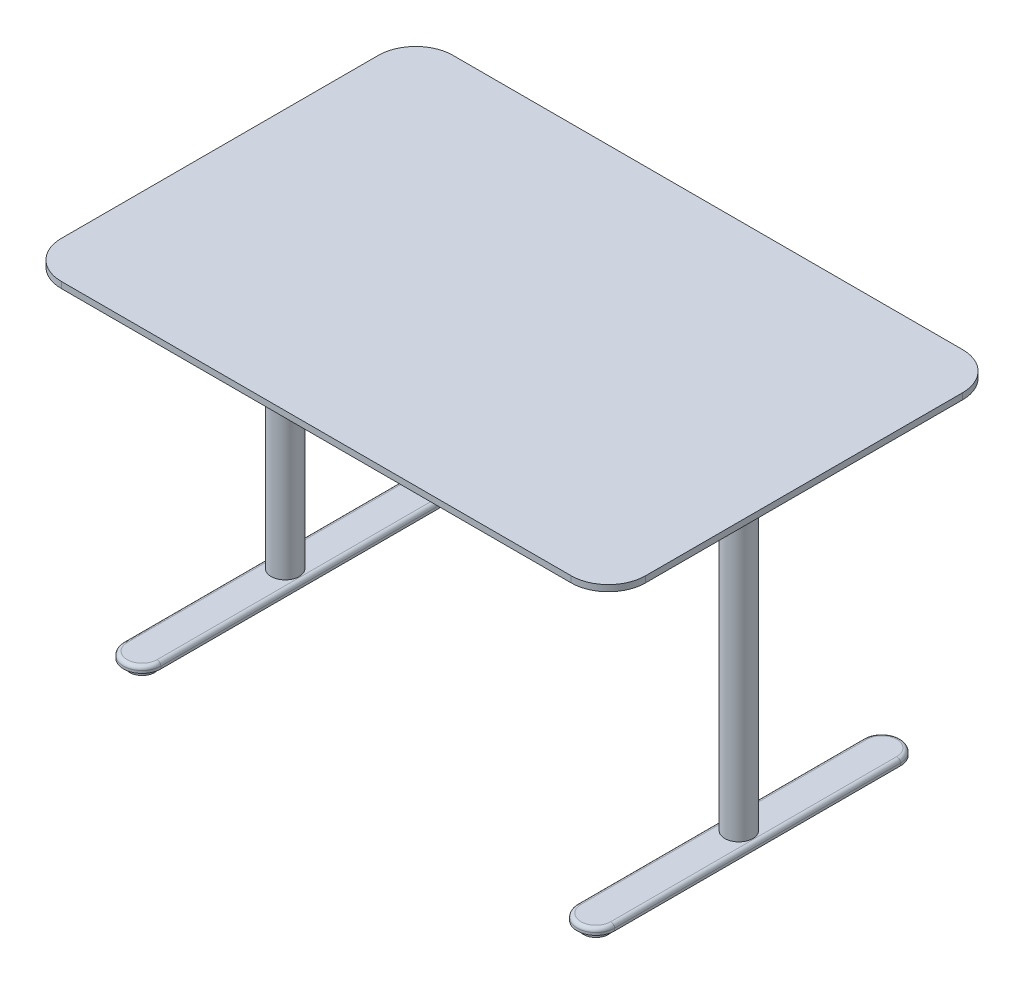
SolidWorks part; units mm, degrees
ref_plane "Front Plane" through (0, 0, 0) normal (0, 0, 1) x (1, 0, 0)
ref_plane "Top Plane" through (0, 0, 0) normal (0, 1, 0) x (1, 0, 0)
ref_plane "Right Plane" through (0, 0, 0) normal (1, 0, 0) x (0, 0, -1)
sketch "Sketch1" plane through (0, 0, 0) normal (0, 1, 0) x (1, 0, 0)
  line L1 (-520.7, 400.05) -> (520.7, 400.05)
  line L2 (-596.9, 323.85) -> (-596.9, -323.85)
  line L3 (-520.7, -400.05) -> (520.7, -400.05)
  line L4 (596.9, 323.85) -> (596.9, -323.85)
  line L5 (-596.9, 400.05) -> (596.9, -400.05) construction
  line L6 (-596.9, -400.05) -> (596.9, 400.05) construction
  arc A0 (-596.9, -323.85) -> (-520.7, -400.05) centre (-520.7, -323.85) ccw
  arc A1 (520.7, -400.05) -> (596.9, -323.85) centre (520.7, -323.85) ccw
  arc A2 (520.7, 400.05) -> (596.9, 323.85) centre (520.7, 323.85) cw
  arc A3 (-520.7, 400.05) -> (-596.9, 323.85) centre (-520.7, 323.85) ccw
  point P0 (0, 0)
  dimension "D3" = 76.2
  dimension "D1" = 1193.8
  dimension "D2" = 800.1
extrude "Boss-Extrude1" add sketch "Sketch1" against normal blind 12.7
sketch "Sketch2" plane through (0, -12.7, 0) normal (0, -1, 0) x (1, 0, 0)
  line L1 (-527.05, 228.6) -> (527.05, 228.6)
  line L2 (-527.05, 228.6) -> (-527.05, -228.6)
  line L3 (-527.05, -228.6) -> (527.05, -228.6)
  line L4 (527.05, 228.6) -> (527.05, -228.6)
  line L5 (-527.05, 228.6) -> (527.05, -228.6) construction
  line L6 (-527.05, -228.6) -> (527.05, 228.6) construction
  point P0 (0, 0)
  dimension "D1" = 1054.1
  dimension "D2" = 457.2
extrude "Extrude-Thin1" add sketch "Sketch2" along normal blind 31.75 separate body thin
sketch "Sketch3" plane through (0, -44.45, 0) normal (0, -1, 0) x (1, 0, 0)
  line L0 (-495.3, -196.85) -> (495.3, -196.85) construction
  line L1 (-431.8, 196.85) -> (-400.05, 196.85)
  line L2 (-431.8, 196.85) -> (-431.8, -196.85)
  line L3 (-431.8, -196.85) -> (-400.05, -196.85)
  line L4 (-400.05, 196.85) -> (-400.05, -196.85)
  line L5 (0, 0) -> (0, 443.3) construction
  line L6 (-495.3, 196.85) -> (-495.3, -196.85) construction
  line L7 (495.3, 196.85) -> (-495.3, 196.85) construction
  line L8 (400.05, 196.85) -> (400.05, -196.85)
  line L9 (431.8, -196.85) -> (400.05, -196.85)
  line L10 (431.8, 196.85) -> (431.8, -196.85)
  line L11 (431.8, 196.85) -> (400.05, 196.85)
  point P11 (-400.05, 196.85)
  dimension "D1" = 31.75
  dimension "D2" = 63.5
extrude "Boss-Extrude3" add sketch "Sketch3" against normal up to surface (31.75 mm away) separate body up to face at (0, -12.7, 0)
sketch "Sketch4" plane through (0, -44.45, 0) normal (0, -1, 0) x (1, 0, 0)
  line L0 (-495.3, 196.85) -> (-495.3, -196.85) construction
  line L1 (-495.3, 44.45) -> (-431.8, 44.45)
  line L2 (-495.3, 44.45) -> (-495.3, -44.45)
  line L3 (-495.3, -44.45) -> (-431.8, -44.45)
  line L4 (-431.8, 44.45) -> (-431.8, -44.45)
  line L5 (-431.8, 196.85) -> (-431.8, -196.85) construction
  line L6 (-431.8, 0) -> (0, 0) construction
  line L7 (0, 0) -> (0, 156.5821) construction
  line L8 (431.8, 44.45) -> (431.8, -44.45)
  line L9 (495.3, -44.45) -> (431.8, -44.45)
  line L10 (495.3, 44.45) -> (495.3, -44.45)
  line L11 (495.3, 44.45) -> (431.8, 44.45)
  dimension "D1" = 88.9
extrude "Boss-Extrude4" add sketch "Sketch4" against normal blind 12.7 separate body
sketch "Sketch5" plane through (0, -44.45, 0) normal (0, -1, 0) x (1, 0, 0)
  line L0 (-463.55, 44.45) -> (-463.55, -44.45) construction
  line L1 (-431.8, 44.45) -> (-495.3, 44.45) construction
  line L2 (-495.3, -44.45) -> (-431.8, -44.45) construction
  line L3 (-463.55, 0) -> (0, 0) construction
  line L4 (0, 0) -> (0, 436.3226) construction
  circle A0 centre (-463.55, 0) radius 28.575
  circle A1 centre (463.55, 0) radius 28.575
  dimension "D1" = 57.15
extrude "Boss-Extrude5" add sketch "Sketch5" along normal blind 635 separate body
sketch "Sketch6" plane through (0, -679.45, 0) normal (0, -1, 0) x (1, 0, 0)
  line L0 (-463.55, -292.1) -> (-463.55, 292.1) construction
  line L1 (-501.65, -292.1) -> (-501.65, 292.1)
  line L2 (-425.45, -292.1) -> (-425.45, 292.1)
  line L3 (0, 0) -> (0, 418.7912) construction
  line L4 (463.55, -292.1) -> (463.55, 292.1) construction
  line L5 (501.65, -292.1) -> (501.65, 292.1)
  line L6 (425.45, -292.1) -> (425.45, 292.1)
  arc A0 (-501.65, -292.1) -> (-425.45, -292.1) centre (-463.55, -292.1) ccw
  arc A1 (-425.45, 292.1) -> (-501.65, 292.1) centre (-463.55, 292.1) ccw
  arc A2 (501.65, -292.1) -> (425.45, -292.1) centre (463.55, -292.1) cw
  arc A3 (425.45, 292.1) -> (501.65, 292.1) centre (463.55, 292.1) cw
  point P2 (-463.55, 0)
  point P13 (463.55, 0)
  dimension "D1" = 76.2
  dimension "D2" = 660.4
extrude "Boss-Extrude6" add sketch "Sketch6" along normal blind 12.7 separate body
sketch "Sketch7" plane through (0, -692.15, 0) normal (0, -1, 0) x (1, 0, 0)
  line L0 (0, 0) -> (0, 464.8967) construction
  line L1 (0, 0) -> (718.3734, 0) construction
  circle A0 centre (-463.55, 292.1) radius 25.4
  circle A1 centre (463.55, 292.1) radius 25.4
  circle A2 centre (463.55, -292.1) radius 25.4
  circle A3 centre (-463.55, -292.1) radius 25.4
  dimension "D1" = 50.8
extrude "Boss-Extrude7" add sketch "Sketch7" along normal blind 12.7 separate body
fillet "Fillet1" radius 7.62 4 edges at (-463.55, -679.45, -330.2) (-501.65, -679.45, 0) (-463.55, -679.45, 330.2) (-425.45, -679.45, 0)
fillet "Fillet2" radius 7.62 4 edges at (463.55, -679.45, 330.2) (501.65, -679.45, 0) (463.55, -679.45, -330.2) (425.45, -679.45, 0)
